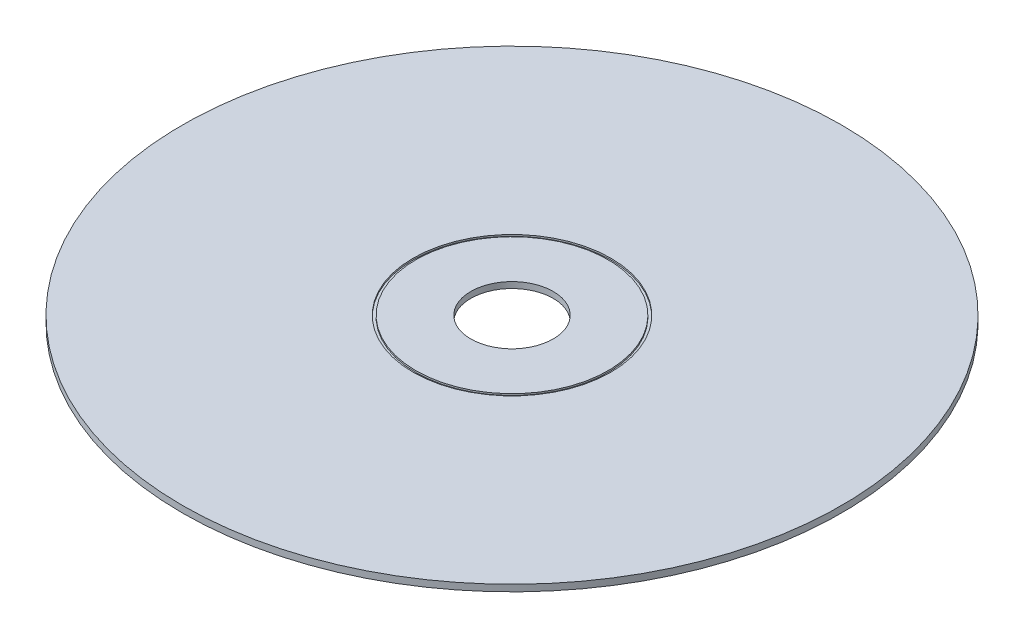
SolidWorks part; units mm, degrees
ref_plane "Front Plane" through (0, 0, 0) normal (0, 0, 1) x (1, 0, 0)
ref_plane "Top Plane" through (0, 0, 0) normal (0, 1, 0) x (1, 0, 0)
ref_plane "Right Plane" through (0, 0, 0) normal (1, 0, 0) x (0, 0, -1)
sketch "Sketch1" plane through (0, 0, 0) normal (0, 1, 0) x (1, 0, 0)
  circle A0 centre (0, 0) radius 60
  circle A1 centre (0, 0) radius 7.5
  dimension "D1" = 120
  dimension "D2" = 15
extrude "Boss-Extrude1" add sketch "Sketch1" along normal blind 1.2
sketch "Sketch2" plane through (0, 1.2, 0) normal (0, 1, 0) x (1, 0, 0)
  circle A0 centre (0, 0) radius 17.5
  circle A1 centre (0, 0) radius 18
  dimension "D1" = 35
  dimension "D2" = 0.5
extrude "Cut-Extrude1" cut sketch "Sketch2" against normal blind 0.3
sketch "Sketch4" plane through (0, 0, 0) normal (0, -1, 0) x (1, 0, 0)
  circle A0 centre (0, 0) radius 17.5
  dimension "D1" = 35
extrude "Cut-Extrude2" cut sketch "Sketch4" against normal blind 0.1
